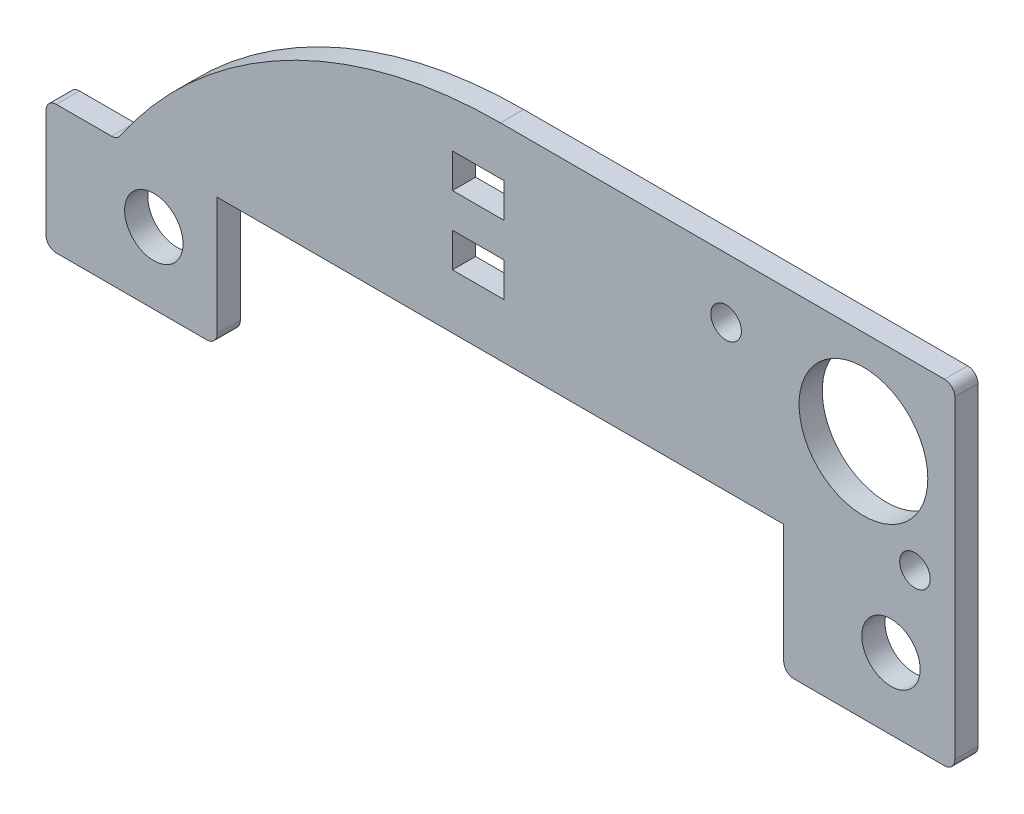
SolidWorks part; units mm, degrees
ref_plane "Front Plane" through (0, 0, 0) normal (0, 0, 1) x (1, 0, 0)
ref_plane "Top Plane" through (0, 0, 0) normal (0, 1, 0) x (1, 0, 0)
ref_plane "Right Plane" through (0, 0, 0) normal (1, 0, 0) x (0, 0, -1)
sketch "Sketch1" plane through (0, 0, 0) normal (0, 0, 1) x (1, 0, 0)
  line L0 (-33.613, 9.245) -> (33.613, 9.245)
  line L2 (26.8526, 27.025) -> (26.8526, 25.12) construction
  line L3 (-33.613, 18.77) -> (-33.613, 9.245)
  line L5 (0, 9.245) -> (0, 0) construction
  line L6 (28.8886, 14.5155) -> (-25.6374, 14.5155) construction
  line L7 (0, 9.245) -> (0, 14.5155) construction
  line L8 (30.6626, 25.12) -> (16.6926, 25.12) construction
  line L10 (30.6626, 20.675) -> (30.6626, 29.565) construction
  line L12 (16.6926, 20.675) -> (16.6926, 29.565) construction
  line L13 (23.6776, 34.01) -> (23.6776, 25.12) construction
  line L16 (33.613, 34.01) -> (0, 34.01)
  line L17 (33.613, 34.01) -> (33.613, 9.245)
  line L18 (-33.613, 18.77) -> (-28.3614, 18.77)
  circle A1 centre (26.8526, 27.025) radius 4.7625
  circle A3 centre (-25.6374, 14.5155) radius 2.159
  circle A4 centre (28.8886, 14.5155) radius 2.159
  circle A5 centre (30.6626, 20.675) radius 1.1303
  circle A6 centre (16.6926, 29.565) radius 1.1303
  arc A8 (0, 34.01) -> (-28.3614, 18.77) centre (0, 0) ccw
  circle A9 centre (0, 0) radius 31.75 construction
  dimension "D6" = 4.318
  dimension "D11" = 2.2606
  dimension "D12" = 9.525
  dimension "D15" = 63.5
  dimension "D18" = 7.9756
  dimension "D4" = 4.7244
  dimension "D2" = 9.525
  dimension "D3" = 67.226
  dimension "D5" = 5.2705
  dimension "D7" = 8.89
  dimension "D8" = 13.97
  dimension "D9" = 8.89
  dimension "D10" = 24.765
  dimension "D13" = 1.905
  dimension "D14" = 3.81
  dimension "D16" = 9.245
  dimension "D17" = 9.9354
extrude "Boss-Extrude1" add sketch "Sketch1" along normal blind 1.7145
sketch "Sketch2" plane through (0, 0, 1.7145) normal (0, 0, 1) x (1, 0, 0)
  line L0 (-1.6441, 29.1667) -> (-1.6441, 24.0867) construction
  line L5 (33.613, 9.245) -> (33.613, 34.01) construction
  line L11 (-3.5491, 29.1667) -> (0.2609, 29.1667) construction
  line L12 (-3.5491, 30.4367) -> (0.2609, 30.4367)
  line L13 (-3.5491, 30.4367) -> (-3.5491, 27.8967)
  line L14 (-3.5491, 27.8967) -> (0.2609, 27.8967)
  line L15 (0.2609, 30.4367) -> (0.2609, 27.8967)
  line L20 (-3.5491, 24.0867) -> (0.2609, 24.0867) construction
  line L21 (-3.5491, 25.3567) -> (0.2609, 25.3567)
  line L22 (-3.5491, 25.3567) -> (-3.5491, 22.8167)
  line L23 (-3.5491, 22.8167) -> (0.2609, 22.8167)
  line L24 (0.2609, 25.3567) -> (0.2609, 22.8167)
  dimension "D5" = 2.54
  dimension "D6" = 3.81
  dimension "D7" = 5.08
extrude "Cut-Extrude1" cut sketch "Sketch2" against normal up to surface (1.7145 mm away) up to face at (-5.0465, 21.2698, 0)
sketch "Sketch3" plane through (0, 0, 1.7145) normal (0, 0, 1) x (1, 0, 0)
  line L0 (-33.613, 9.245) -> (33.613, 9.245) construction
  line L1 (-20.955, 18.77) -> (20.955, 18.77)
  line L2 (-20.955, 18.77) -> (-20.955, 9.245)
  line L3 (-20.955, 9.245) -> (20.955, 9.245)
  line L4 (20.955, 18.77) -> (20.955, 9.245)
  line L5 (0, 9.245) -> (0, 0) construction
  line L6 (0, 9.245) -> (0, 14.5155) construction
  point P6 (0, 9.245)
  dimension "D1" = 9.525
  dimension "D2" = 41.91
extrude "Cut-Extrude2" cut sketch "Sketch3" against normal up to surface (1.7145 mm away) up to face at (-1.6441, 29.1667, 0)
fillet "Fillet1" radius 0.762 7 edges at (33.613, 34.01, 0.8573) (33.613, 9.245, 0.8573) (-33.613, 9.245, 0.8573) (-28.3614, 18.77, 0.8573) (-33.613, 18.77, 0.8573) (20.955, 9.245, 0.8573) (-20.955, 9.245, 0.8573)
